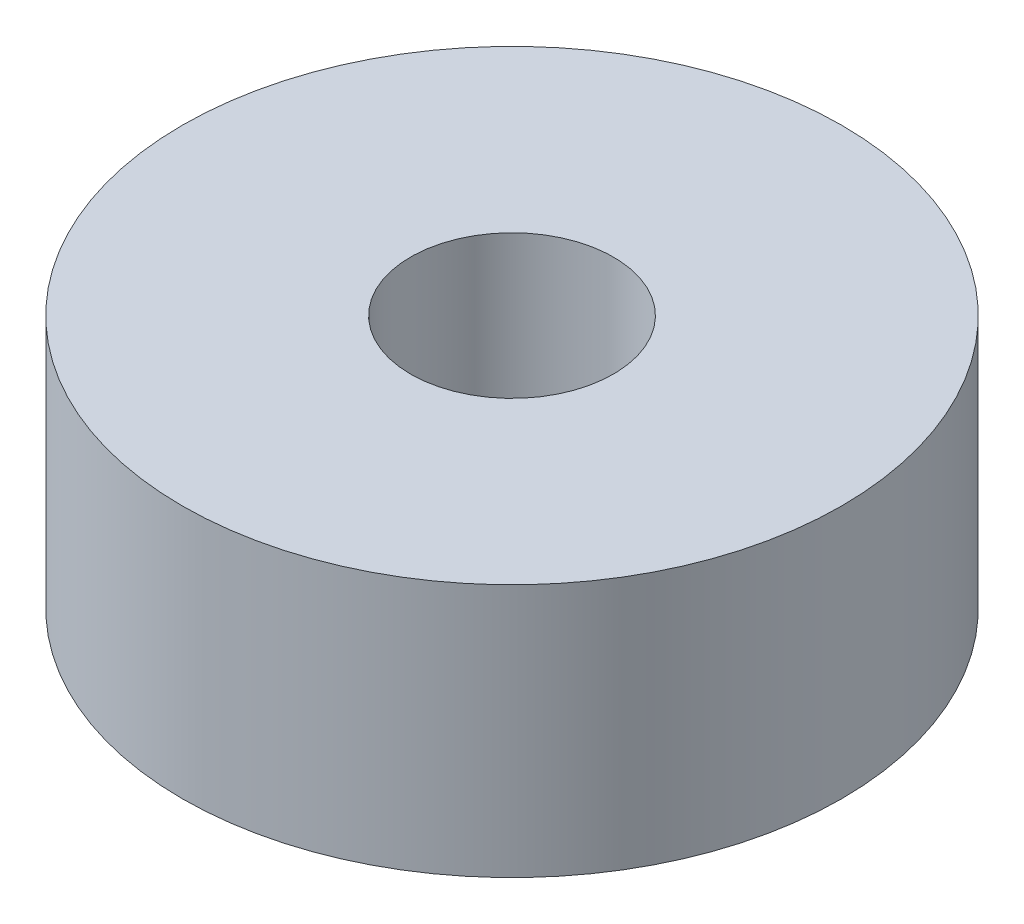
SolidWorks part; units mm, degrees
ref_plane "前视基准面" through (0, 0, 0) normal (0, 0, 1) x (1, 0, 0)
ref_plane "上视基准面" through (0, 0, 0) normal (0, 1, 0) x (1, 0, 0)
ref_plane "右视基准面" through (0, 0, 0) normal (1, 0, 0) x (0, 0, -1)
sketch "草图1" plane through (0, 0, 0) normal (0, 1, 0) x (1, 0, 0)
  circle A0 centre (0, 0) radius 2
  circle A1 centre (0, 0) radius 6.5
  dimension "D1" = 13
  dimension "D2" = 4
extrude "凸台-拉伸1" add sketch "草图1" along normal blind 5
